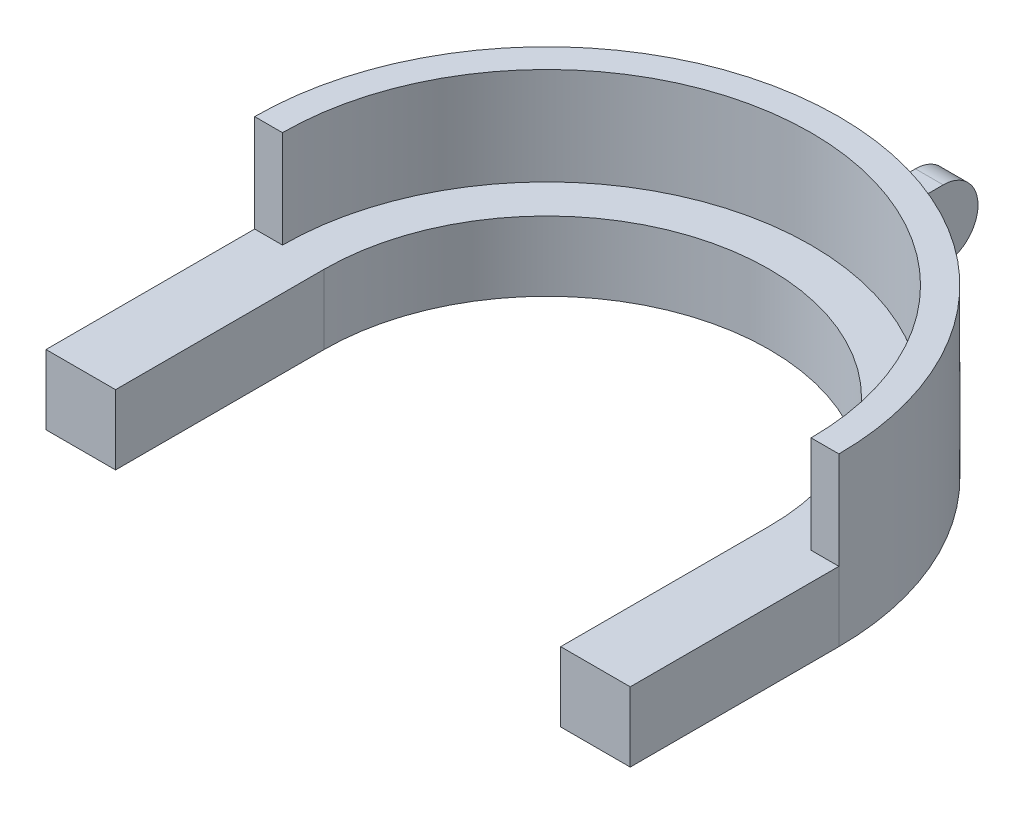
SolidWorks part; units mm, degrees
ref_plane "前视基准面" through (0, 0, 0) normal (0, 0, 1) x (1, 0, 0)
ref_plane "上视基准面" through (0, 0, 0) normal (0, 1, 0) x (1, 0, 0)
ref_plane "右视基准面" through (0, 0, 0) normal (1, 0, 0) x (0, 0, -1)
sketch "草图1" plane through (0, 0, 0) normal (0, 1, 0) x (1, 0, 0)
  line L0 (-42.0171, 0) -> (60.0376, 0) construction
  line L1 (-38, 0) -> (-32, 0)
  line L2 (32, 0) -> (38, 0)
  arc A0 (32, 0) -> (-32, 0) centre (0, 0) ccw
  arc A1 (38, 0) -> (-38, 0) centre (0, 0) ccw
extrude "凸台-拉伸1" add sketch "草图1" along normal blind 10
sketch "草图2" plane through (0, 0, 0) normal (0, -1, 0) x (1, 0, 0)
  line L0 (32, 0) -> (38, 0) construction
  line L1 (-38, 0) -> (-42, 0)
  line L2 (38, 0) -> (42, 0)
  arc A0 (-38, 0) -> (38, 0) centre (0, 0) ccw
  arc A1 (-38, 0) -> (38, 0) centre (0, 0) ccw construction
  arc A2 (-42, 0) -> (42, 0) centre (0, 0) ccw
extrude "凸台-拉伸2" add sketch "草图2" against normal blind 24
sketch "草图3" plane through (0, 0, 0) normal (0, -1, 0) x (1, 0, 0)
  line L0 (0, 0) -> (0, -64.6411) construction
  line L1 (0, 0) -> (2, 1.1547) construction
  line L2 (0, 0) -> (-2, 1.1547) construction
  line L3 (2, -64.6411) -> (2, 21.9083) construction
  line L4 (-2, -64.6411) -> (-2, 17.1602) construction
  line L5 (51.9615, 30) -> (57.0648, 32.9464) construction
  line L6 (-2, -36) -> (2, -36)
  line L7 (-2, -36) -> (-2, -60)
  line L8 (-2, -60) -> (2, -60)
  line L9 (2, -36) -> (2, -60)
  line L10 (-42, 0) -> (-32, 0) construction
  line L11 (-9.9586, -11.5231) -> (2, -4.6188) construction
  line L12 (-32, 0) -> (-32, 30)
  line L13 (54.2808, 25.5655) -> (66.0822, 32.3791) construction
  line L14 (56.2348, 20.9201) -> (69.2986, 28.4625) construction
  line L15 (-42, 0) -> (-42, 30)
  line L16 (32, 0) -> (42, 0) construction
  line L17 (-6.9702, -15.5713) -> (2, -10.3923) construction
  line L18 (32, 0) -> (32, 30)
  line L19 (-42, 0) -> (-32, 0)
  line L20 (42, 0) -> (42, 30)
  line L21 (32, 0) -> (42, 0)
  line L22 (56.7808, 21.2354) -> (56.2348, 20.9201)
  line L23 (-42, 30) -> (-32, 30)
  line L24 (32, 30) -> (42, 30)
  line L25 (-2, -4.6188) -> (4.3785, -8.3014) construction
  arc A0 (-56.2348, 20.9201) -> (56.2348, 20.9201) centre (0, 0) ccw construction
  arc A1 (54.2808, 25.5655) -> (-51.9615, 30) centre (0, 0) ccw construction
  dimension "D1" = 2
  dimension "D2" = 2
  dimension "D3" = 36
  dimension "D4" = 24
  dimension "D5" = 30
  dimension "D6" = 30
  dimension "D7" = 5
  dimension "D8" = 5
extrude "凸台-拉伸3" add sketch "草图3" against normal blind 10
sketch "草图4" plane through (-2, 0, 0) normal (-1, 0, 0) x (0, 0, 1)
  line L1 (-55, 10) -> (-63.2304, 10)
  line L3 (-55, 0) -> (-63.2304, 0)
  line L4 (-63.2304, 10) -> (-63.2304, 0)
  arc A0 (-55, 10) -> (-55, 0) centre (-55, 5) ccw
extrude "切除-拉伸1" cut sketch "草图4" against normal blind 10
